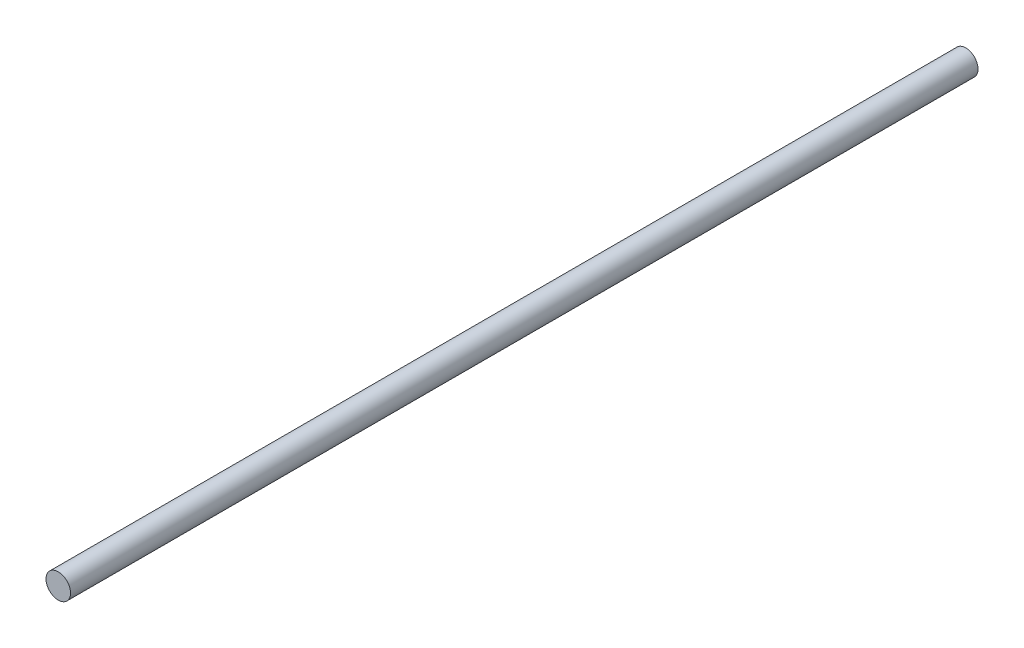
SolidWorks part; units mm, degrees
ref_plane "Front Plane" through (0, 0, 0) normal (0, 0, 1) x (1, 0, 0)
ref_plane "Top Plane" through (0, 0, 0) normal (0, 1, 0) x (1, 0, 0)
ref_plane "Right Plane" through (0, 0, 0) normal (1, 0, 0) x (0, 0, -1)
sketch "Sketch1" plane through (0, 0, 0) normal (0, 0, 1) x (1, 0, 0)
  circle A0 centre (0, 0) radius 4
  dimension "D1" = 8
extrude "Boss-Extrude1" add sketch "Sketch1" along normal blind 287.5
sketch "Sketch2" plane through (0, 0, 287.5) normal (0, 0, 1) x (1, 0, 0)
  circle A1 centre (0, 0) radius 4
  circle A2 centre (0, 0) radius 4
  dimension "D1" = 0
extrude "Boss-Extrude2" add sketch "Sketch2" along normal blind 45
sketch "Sketch3" plane through (0, 0, 0) normal (0, 0, -1) x (-1, 0, 0)
  circle A1 centre (0, 0) radius 4
  circle A2 centre (0, 0) radius 4
  dimension "D1" = 0
extrude "Cut-Extrude1" cut sketch "Sketch3" against normal blind 105
sketch "Sketch4" plane through (0, 0, 105) normal (0, 0, -1) x (-1, 0, 0)
  circle A1 centre (0, 0) radius 4
  circle A2 centre (0, 0) radius 4
  dimension "D1" = 0
extrude "Boss-Extrude3" add sketch "Sketch4" along normal blind 68.5
